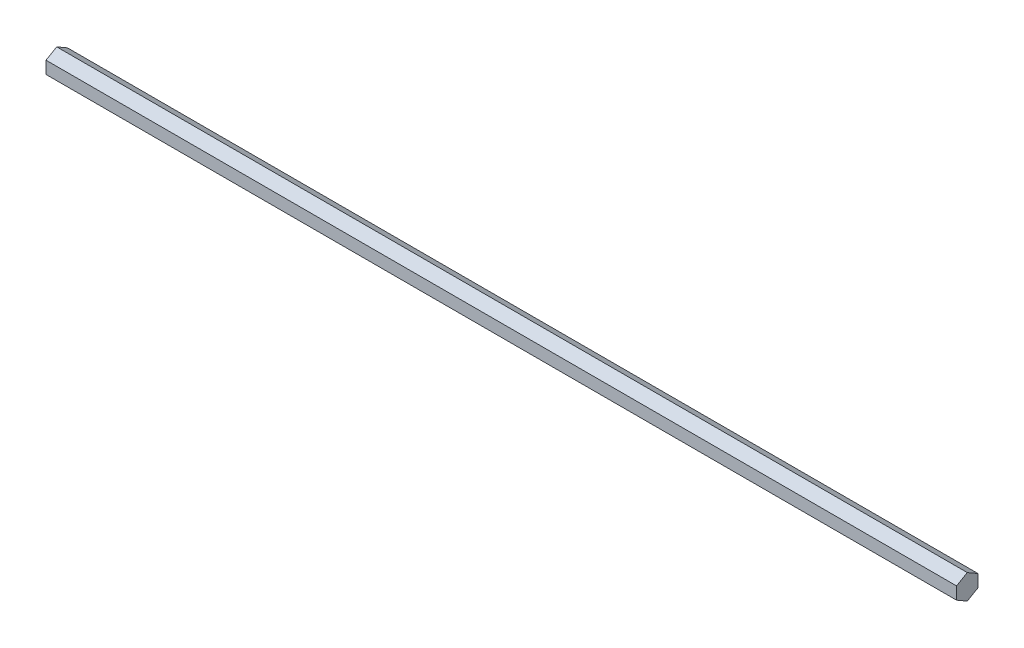
SolidWorks part; units mm, degrees
ref_plane "Front" through (0, 0, 0) normal (0, 0, 1) x (1, 0, 0)
ref_plane "Top" through (0, 0, 0) normal (0, 1, 0) x (1, 0, 0)
ref_plane "Right" through (0, 0, 0) normal (1, 0, 0) x (0, 0, -1)
sketch "Sketch1" plane through (0, 0, 0) normal (1, 0, 0) x (0, 0, -1)
  line L1 (0, 7.3323) -> (-6.35, 3.6662)
  line L2 (-6.35, 3.6662) -> (-6.35, -3.6662)
  line L3 (-6.35, -3.6662) -> (0, -7.3323)
  line L4 (0, -7.3323) -> (6.35, -3.6662)
  line L5 (6.35, -3.6662) -> (6.35, 3.6662)
  line L6 (6.35, 3.6662) -> (0, 7.3323)
  circle A0 centre (0, 0) radius 6.35 construction
  dimension "D1" = 12.7
extrude "Boss-Extrude1" add sketch "Sketch1" along normal blind 539.75
